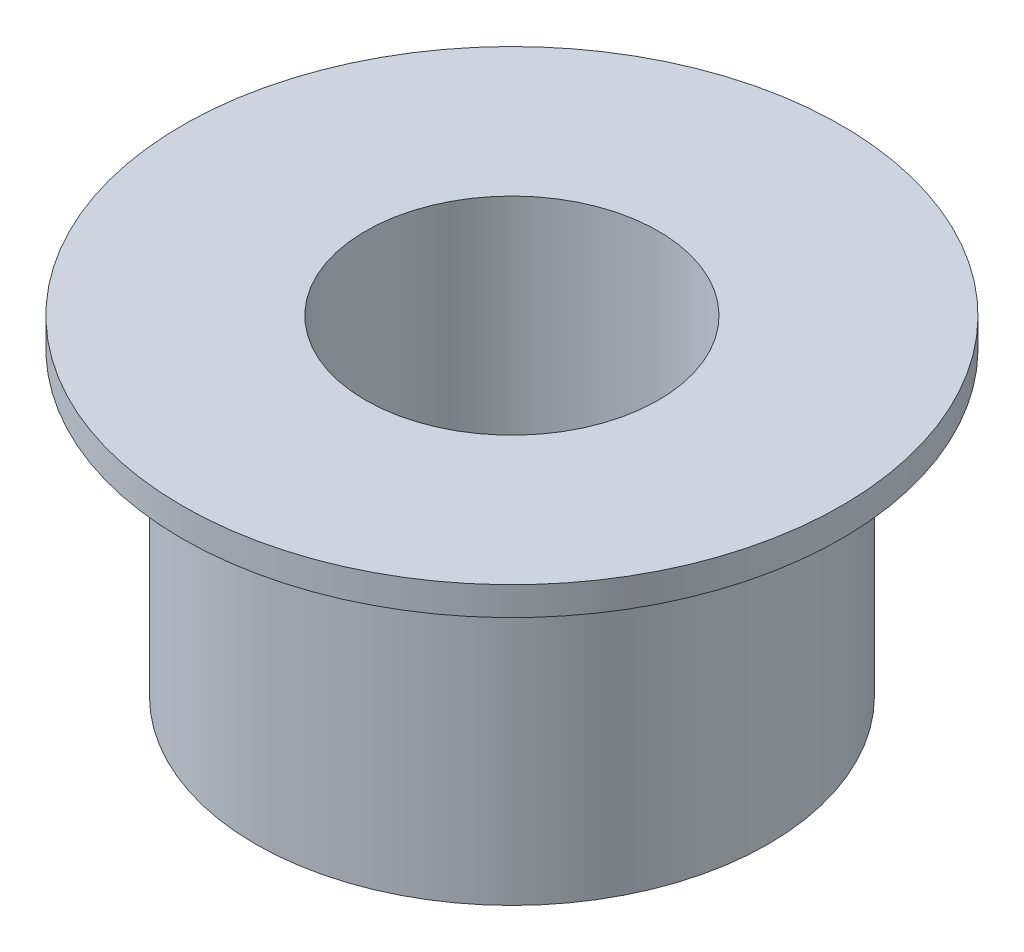
SolidWorks part; units mm, degrees
ref_plane "Front Plane" through (0, 0, 0) normal (0, 0, 1) x (1, 0, 0)
ref_plane "Top Plane" through (0, 0, 0) normal (0, 1, 0) x (1, 0, 0)
ref_plane "Right Plane" through (0, 0, 0) normal (1, 0, 0) x (0, 0, -1)
sketch "Sketch1" plane through (0, 0, 0) normal (1, 0, 0) x (0, 0, -1)
  line L0 (0, 4.5) -> (0, -4.5) construction
  line L1 (0, -4.5) -> (0, -3.1173) construction
  line L2 (7, -4.5) -> (4, -2.5)
  line L3 (4, -2.5) -> (4, 4.5)
  line L4 (4, 4.5) -> (9, 4.5)
  line L5 (9, 4.5) -> (9, 3.7217)
  line L6 (9, 3.7217) -> (7, 3.7217)
  line L7 (7, 3.7217) -> (7, -4.5)
  point P6 (0, 0)
  point P11 (0, 0)
  dimension "D1" = 9
  dimension "D2" = 9
  dimension "D3" = 7
  dimension "D4" = 4
  dimension "D5" = 2
revolve "Revolve1" add sketch "Sketch1" angle 360 about L0
